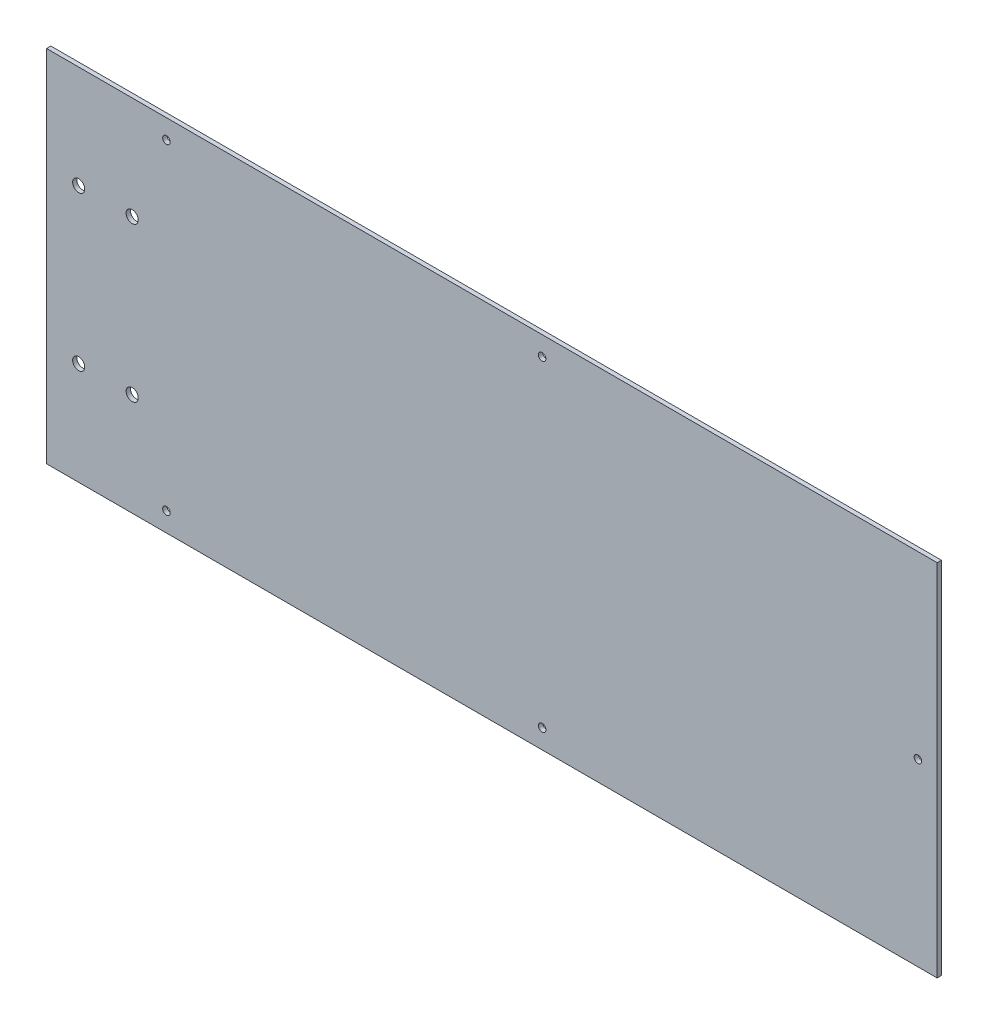
SolidWorks part; units mm, degrees
ref_plane "Front Plane" through (0, 0, 0) normal (0, 0, 1) x (1, 0, 0)
ref_plane "Top Plane" through (0, 0, 0) normal (0, 1, 0) x (1, 0, 0)
ref_plane "Right Plane" through (0, 0, 0) normal (1, 0, 0) x (0, 0, -1)
sketch "Sketch1" plane through (0, 0, 0) normal (0, 0, 1) x (1, 0, 0)
  line L0 (31.75, 133.35) -> (31.75, 0) construction
  line L1 (0, 0) -> (330.2, 0)
  line L2 (0, 0) -> (0, 133.35)
  line L3 (0, 133.35) -> (330.2, 133.35)
  line L4 (330.2, 0) -> (330.2, 133.35)
  line L5 (0, 95.25) -> (330.2, 95.25) construction
  line L7 (0, 38.1) -> (330.2, 38.1) construction
  circle A0 centre (323.0626, 66.675) radius 1.397
  circle A1 centre (183.7436, 126.2126) radius 1.397
  circle A2 centre (44.45, 126.2126) radius 1.397
  circle A3 centre (183.7436, 7.1374) radius 1.397
  circle A4 centre (44.45, 7.1374) radius 1.397
  circle A5 centre (11.9126, 95.25) radius 2.2479
  circle A6 centre (11.9126, 38.1) radius 2.2479
  circle A7 centre (31.75, 95.25) radius 2.2479
  circle A8 centre (31.75, 38.1) radius 2.2479
  dimension "D6" = 139.2936
  dimension "D2" = 146.4564
  dimension "D8" = 38.1
  dimension "D1" = 66.675
  dimension "D3" = 31.75
  dimension "D9" = 95.25
extrude "Boss-Extrude1" add sketch "Sketch1" along normal blind 1.5875
